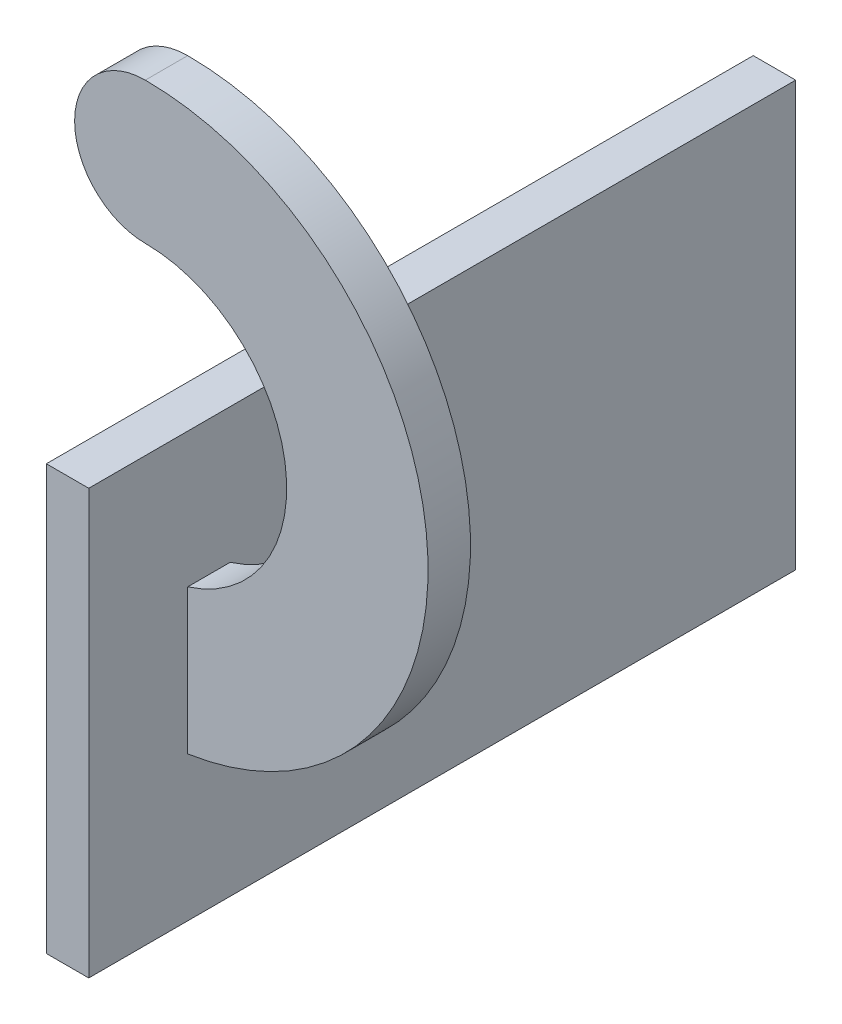
SolidWorks part; units mm, degrees
ref_plane "Front Plane" through (0, 0, 0) normal (0, 0, 1) x (1, 0, 0)
ref_plane "Top Plane" through (0, 0, 0) normal (0, 1, 0) x (1, 0, 0)
ref_plane "Right Plane" through (0, 0, 0) normal (1, 0, 0) x (0, 0, -1)
sketch "Sketch1" plane through (0, 0, 0) normal (0, 0, 1) x (1, 0, 0)
  line L0 (0, 0) -> (0, -10)
  line L1 (0, 20) -> (0, 10)
  line L2 (0, -10) -> (0, -20)
  circle A0 centre (0, 0) radius 20
  circle A1 centre (0, 0) radius 10
  circle A2 centre (0, 15) radius 5
  dimension "D1" = 40
  dimension "D2" = 20
extrude "Boss-Extrude1" add sketch "Sketch1" along normal blind 3 contours L1 A2 | L1 A2 | A2 A1 L2 A0
sketch "Sketch2" plane through (0, 0, 0) normal (-1, 0, 0) x (0, 0, 1)
  line L1 (0, -10) -> (3, -10)
  line L2 (0, -10) -> (0, -20)
  line L3 (0, -20) -> (3, -20)
  line L4 (3, -10) -> (3, -20)
extrude "Boss-Extrude2" add sketch "Sketch2" against normal blind 3
sketch "Sketch3" plane through (0, -20, 0) normal (0, -1, 0) x (1, 0, 0)
  line L1 (0, 3) -> (3, 3)
  line L2 (0, 3) -> (0, 0)
  line L3 (0, 0) -> (3, 0)
  line L4 (3, 3) -> (3, 0)
extrude "Boss-Extrude3" add sketch "Sketch3" against normal blind 20
sketch "Sketch4" plane through (0, -20, 0) normal (0, -1, 0) x (-1, 0, 0)
  line L1 (0, -3) -> (-3, -3)
  line L2 (0, -3) -> (0, 0)
  line L3 (0, 0) -> (-3, 0)
  line L4 (-3, -3) -> (-3, 0)
extrude "Boss-Extrude4" add sketch "Sketch4" along normal blind 10
sketch "Sketch5" plane through (0, 0, 0) normal (0, 0, -1) x (-1, 0, 0)
  line L0 (0, -30) -> (-3, -30) construction
  line L1 (0, 0) -> (-3, 0)
  line L2 (0, 0) -> (0, -30)
  line L3 (0, -30) -> (-3, -30)
  line L4 (-3, 0) -> (-3, -30)
  line L5 (-3, -19.7737) -> (-3, -30) construction
  point P7 (-1.5, -30)
  dimension "D1" = 0
  dimension "D2" = 0
extrude "Boss-Extrude5" add sketch "Sketch5" along normal blind 40
sketch "Sketch6" plane through (0, 0, 3) normal (0, 0, 1) x (1, 0, 0)
  line L1 (0, 0) -> (3, 0)
  line L2 (0, 0) -> (0, -30)
  line L3 (0, -30) -> (3, -30)
  line L4 (3, 0) -> (3, -30)
extrude "Boss-Extrude6" add sketch "Sketch6" along normal blind 7
